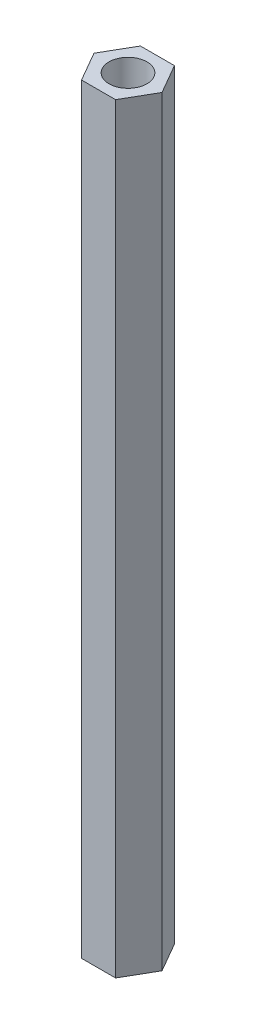
SolidWorks part; units mm, degrees
ref_plane "Front Plane" through (0, 0, 0) normal (0, 0, 1) x (1, 0, 0)
ref_plane "Top Plane" through (0, 0, 0) normal (0, 1, 0) x (1, 0, 0)
ref_plane "Right Plane" through (0, 0, 0) normal (1, 0, 0) x (0, 0, -1)
sketch "Sketch1" plane through (0, 0, 0) normal (0, 1, 0) x (1, 0, 0)
  line L0 (1.3414, 2.3233) -> (2.6828, 0)
  line L1 (-1.3414, 2.3233) -> (1.3414, 2.3233)
  line L2 (2.6828, 0) -> (1.3414, -2.3233)
  line L3 (1.3414, -2.3233) -> (-1.3414, -2.3233)
  line L4 (-1.3414, -2.3233) -> (-2.6828, 0)
  line L5 (-2.6828, 0) -> (-1.3414, 2.3233)
  circle A0 centre (0, 0) radius 1.5
  dimension "D1" = 3
  dimension "D3" = 6
extrude "Boss-Extrude1" add sketch "Sketch1" along normal blind 60
